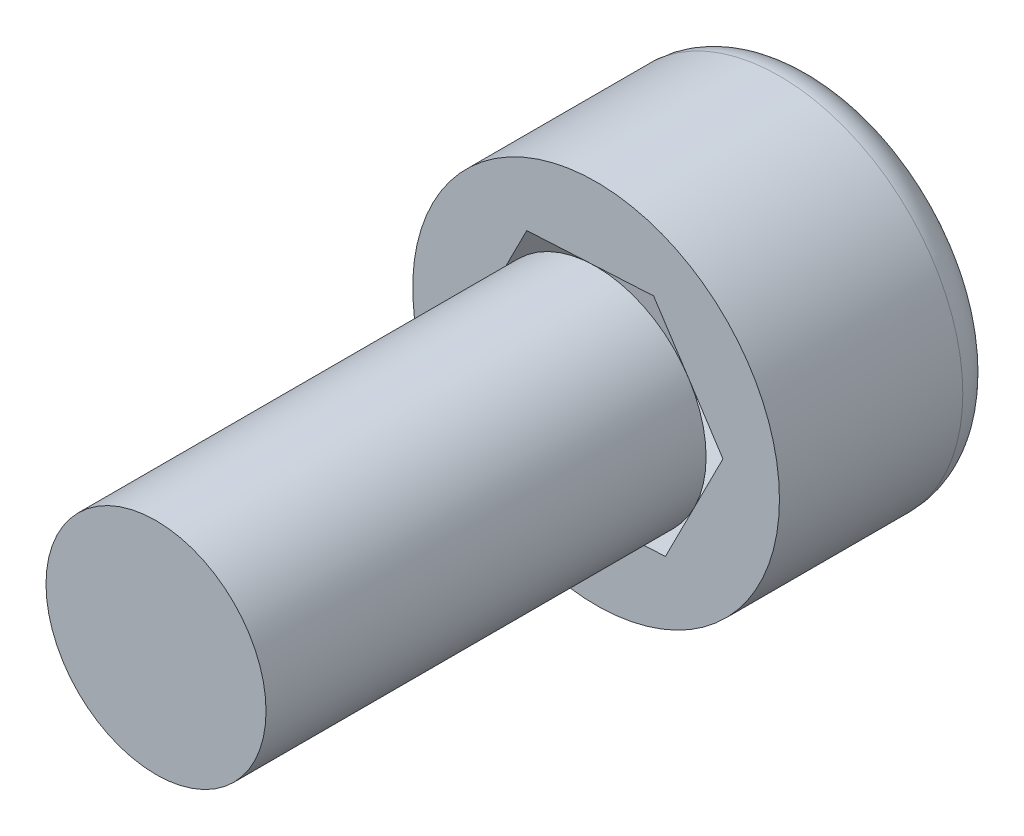
SolidWorks part; units mm, degrees
ref_plane "Front Plane" through (0, 0, 0) normal (0, 0, 1) x (1, 0, 0)
ref_plane "Top Plane" through (0, 0, 0) normal (0, 1, 0) x (1, 0, 0)
ref_plane "Right Plane" through (0, 0, 0) normal (1, 0, 0) x (0, 0, -1)
sketch "Sketch1" plane through (0, 0, 0) normal (0, 0, 1) x (1, 0, 0)
  circle A0 centre (0, 0) radius 2.5
  dimension "D1" = 5
extrude "Boss-Extrude1" add sketch "Sketch1" along normal blind 3
sketch "Sketch2" plane through (0, 0, 3) normal (0, 0, 1) x (1, 0, 0)
  circle A0 centre (0, 0) radius 1.5
  dimension "D1" = 3
extrude "Boss-Extrude2" add sketch "Sketch2" along normal blind 6
sketch "Sketch3" plane through (0, 0, 0) normal (0, 0, -1) x (-1, 0, 0)
  line L1 (0.7845, -1.5442) -> (1.7296, -0.0927)
  line L2 (1.7296, -0.0927) -> (0.9451, 1.4515)
  line L3 (0.9451, 1.4515) -> (-0.7845, 1.5442)
  line L4 (-0.7845, 1.5442) -> (-1.7296, 0.0927)
  line L5 (-1.7296, 0.0927) -> (-0.9451, -1.4515)
  line L6 (-0.9451, -1.4515) -> (0.7845, -1.5442)
  circle A0 centre (0, 0) radius 1.5 construction
  dimension "D1" = 3
extrude "Cut-Extrude1" cut sketch "Sketch3" against normal blind 3
fillet "Fillet1" radius 0.5 1 edges at (2.5, 0, 0)
